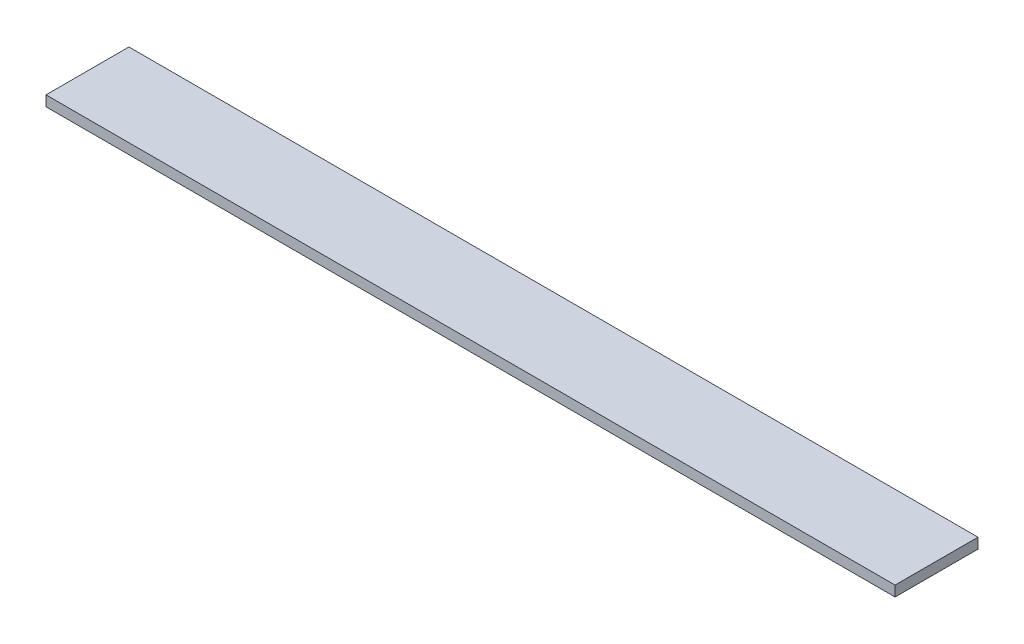
SolidWorks part; units mm, degrees
ref_plane "Front Plane" through (0, 0, 0) normal (0, 0, 1) x (1, 0, 0)
ref_plane "Top Plane" through (0, 0, 0) normal (0, 1, 0) x (1, 0, 0)
ref_plane "Right Plane" through (0, 0, 0) normal (1, 0, 0) x (0, 0, -1)
sketch "Sketch1" plane through (0, 0, 0) normal (0, 1, 0) x (1, 0, 0)
  line L1 (0, 0) -> (260.096, 0)
  line L2 (0, 0) -> (0, 25.4)
  line L3 (0, 25.4) -> (260.096, 25.4)
  line L4 (260.096, 0) -> (260.096, 25.4)
  dimension "D1" = 25.4
  dimension "D2" = 260.096
extrude "Boss-Extrude1" add sketch "Sketch1" along normal blind 3.175
